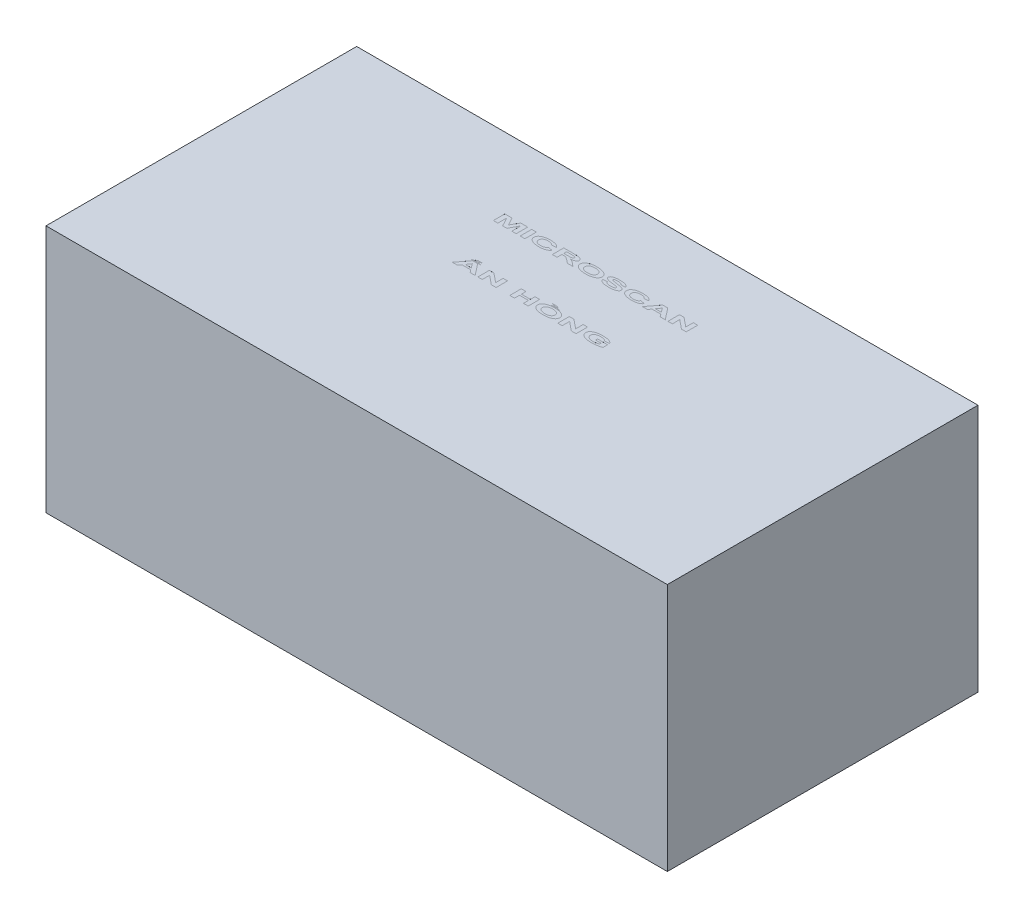
SolidWorks part; units mm, degrees
ref_plane "Front Plane" through (0, 0, 0) normal (0, 0, 1) x (1, 0, 0)
ref_plane "Top Plane" through (0, 0, 0) normal (0, 1, 0) x (1, 0, 0)
ref_plane "Right Plane" through (0, 0, 0) normal (1, 0, 0) x (0, 0, -1)
sketch "Sketch1" plane through (0, 0, 0) normal (0, 0, 1) x (1, 0, 0)
  line L1 (500, -200) -> (-500, -200)
  line L2 (500, -200) -> (500, 200)
  line L3 (500, 200) -> (-500, 200)
  line L4 (-500, -200) -> (-500, 200)
  line L5 (500, -200) -> (-500, 200) construction
  line L6 (500, 200) -> (-500, -200) construction
  point P0 (0, 0)
  dimension "D1" = 400
  dimension "D2" = 1000
extrude "Boss-Extrude1" add sketch "Sketch1" along normal blind 500
sketch "Sketch2" plane through (0, 200, 0) normal (0, 1, 0) x (1, 0, 0)
  text T0 "<b>MICROSCAN</b>\r\n\r\n\r\n<b>  ẤN HỒNG</b>" font "Arial" height in points 72
extrude "Cut-Extrude1" cut sketch "Sketch2" against normal blind 0.01
